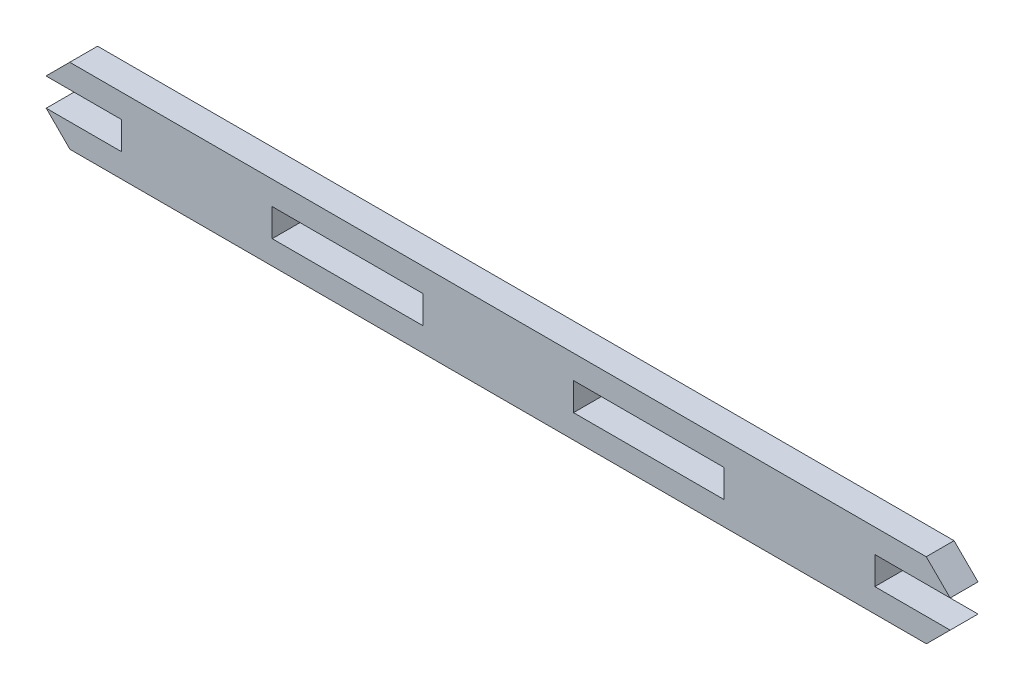
SolidWorks part; units mm, degrees
ref_plane "Front Plane" through (0, 0, 0) normal (0, 0, 1) x (1, 0, 0)
ref_plane "Top Plane" through (0, 0, 0) normal (0, 1, 0) x (1, 0, 0)
ref_plane "Right Plane" through (0, 0, 0) normal (1, 0, 0) x (0, 0, -1)
sketch "Sketch2" plane through (0, 0, 0) normal (0, 0, 1) x (1, 0, 0)
  line L5 (55.6117, 15.146) -> (226.1517, 15.146)
  line L35 (140.8817, 15.146) -> (140.959, 0.146) construction
  line L40 (55.6503, 0.146) -> (226.1903, 0.146)
  line L42 (155.9223, 10.416) -> (185.9223, 10.416)
  line L43 (155.9223, 10.416) -> (155.9223, 4.876)
  line L44 (155.9223, 4.876) -> (185.9223, 4.876)
  line L45 (185.9223, 10.416) -> (185.9223, 4.876)
  line L57 (50.8817, 10.416) -> (55.6117, 15.146)
  line L58 (50.9223, 4.876) -> (55.6503, 0.146)
  line L59 (226.1903, 0.146) -> (230.9223, 4.876)
  line L60 (226.1517, 15.146) -> (230.9223, 10.416)
  line L62 (95.9223, 10.416) -> (95.9223, 4.876)
  line L63 (95.9223, 10.416) -> (125.9223, 10.416)
  line L64 (125.9223, 10.416) -> (125.9223, 4.876)
  line L65 (95.9223, 4.876) -> (125.9223, 4.876)
  line L67 (50.9223, 4.876) -> (65.9223, 4.876)
  line L69 (50.8817, 10.416) -> (65.9223, 10.416)
  line L70 (65.9223, 4.876) -> (65.9223, 10.416)
  line L71 (230.9223, 4.876) -> (215.9223, 4.876)
  line L73 (230.9223, 10.416) -> (215.9223, 10.416)
  line L74 (215.9223, 4.876) -> (215.9223, 10.416)
  point P0 (50.8817, 15.146)
  point P1 (230.9203, 0.146)
  point P2 (50.9203, 0.146)
  point P3 (230.8817, 15.1459)
  dimension "D2" = 15
  dimension "D3" = 4.73
  dimension "D4" = 5.54
  dimension "D5" = 30
  dimension "D6" = 30
  dimension "D8" = 2
  dimension "D9" = 30
  dimension "D10" = 15
  dimension "D11" = 30
  dimension "D12" = 15
  dimension "D7" = 15
  dimension "D13" = 170.54
  dimension "D14" = 170.54
extrude "Boss-Extrude1" add sketch "Sketch2" along normal blind 5.54
